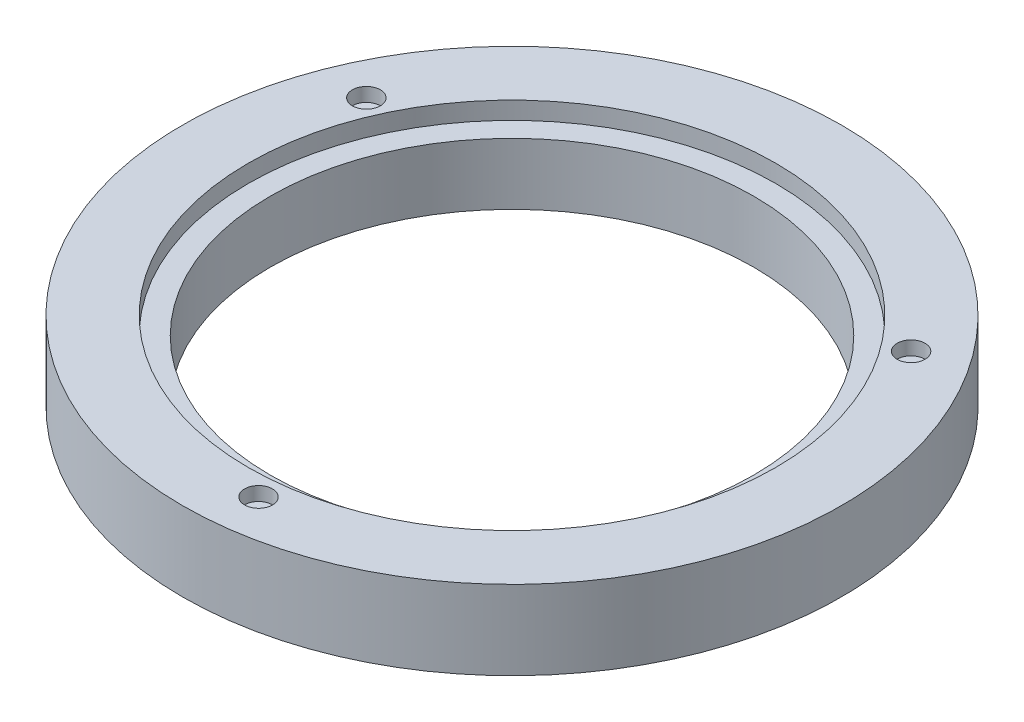
SolidWorks part; units mm, degrees
ref_plane "Plan de face" through (0, 0, 0) normal (0, 0, 1) x (1, 0, 0)
ref_plane "Plan de dessus" through (0, 0, 0) normal (0, 1, 0) x (1, 0, 0)
ref_plane "Plan de droite" through (0, 0, 0) normal (1, 0, 0) x (0, 0, -1)
sketch "Esquisse1" plane through (0, 0, 0) normal (0, 1, 0) x (1, 0, 0)
  circle A0 centre (0, 0) radius 75
  circle A1 centre (0, 0) radius 55
extrude "Boss.-Extru.3" add sketch "Esquisse1" along normal blind 18
sketch "Esquisse6" plane through (0, 18, 0) normal (0, 1, 0) x (1, 0, 0)
  circle A1 centre (0, 0) radius 55 construction
  circle A2 centre (0, 0) radius 60
  circle A3 centre (0, 0) radius 60
  circle A4 centre (0, 0) radius 55
extrude "Enlèv. mat.-Extru.2" cut sketch "Esquisse6" against normal blind 4
ref_plane "Plan1" through (0, 9, 0) normal (0, 1, 0) x (1, 0, 0)
sketch "Esquisse5" plane through (0, 18, 0) normal (0, 1, 0) x (1, 0, 0)
  circle A0 centre (-59.4418, 26.2996) radius 3.175
  circle A1 centre (0, 0) radius 75 construction
  circle A4 centre (52.497, 38.3283) radius 3.175
  circle A5 centre (6.9448, -64.6279) radius 3.175
  point P13 (0, 0)
extrude "Enlèv. mat.-Extru.1" cut sketch "Esquisse5" against normal blind 3.15
sketch "Esquisse9" plane through (0, 0, 0) normal (0, -1, 0) x (1, 0, 0)
  circle A0 centre (59.4418, 26.2996) radius 3.175
  circle A4 centre (-6.9448, -64.6279) radius 3.175
  circle A5 centre (-52.497, 38.3283) radius 3.175
  point P11 (0, 0)
extrude "Enlèv. mat.-Extru.3" cut sketch "Esquisse9" against normal blind 3.15
equation "\"outer_diameter\"= 150"
equation "\"inner_diameter\"= 110"
equation "\"inner_offset\"= 5"
equation "\"magnet_diameter\"= 6.35"
equation "\"magnet_hieght\"= 3.15"
equation "\"D1@Esquisse1\"=\"outer_diameter\""
equation "\"ring_height\"= 18"
equation "\"magnet_slot_offset\"= 5"
equation "\"D2@Esquisse1\"=\"inner_diameter\""
equation "\"D1@Boss.-Extru.3\"=\"ring_height\""
equation "\"D1@Esquisse5\"=\"magnet_diameter\""
equation "\"D2@Esquisse5\"=(\"outer_diameter\"-(\"outer_diameter\"-\"inner_diameter\")/2)/2"
equation "\"D1@Enlèv. mat.-Extru.1\"=\"magnet_hieght\""
equation "\"D2@Esquisse6\"=\"inner_diameter\""
equation "\"D1@Esquisse9\"=\"magnet_diameter\""
equation "\"D1@Enlèv. mat.-Extru.3\"=\"magnet_hieght\""
